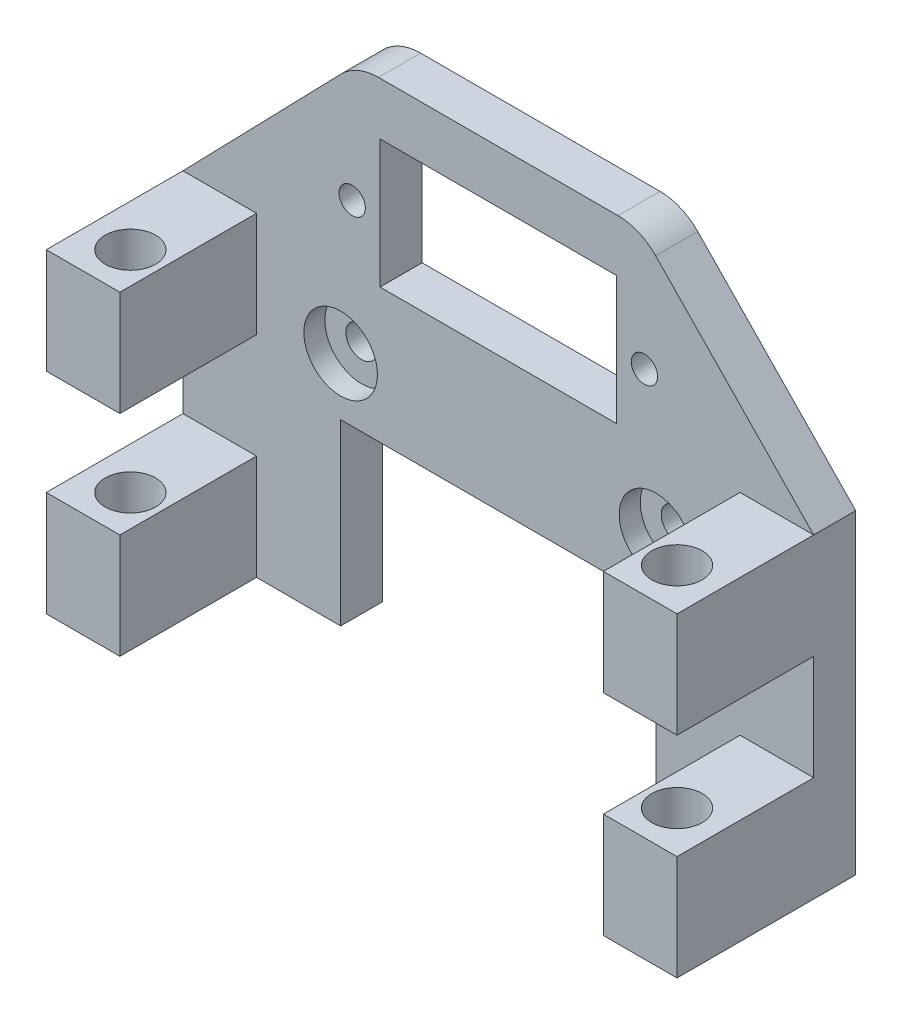
SolidWorks part; units mm, degrees
ref_plane "前视基准面" through (0, 0, 0) normal (0, 0, 1) x (1, 0, 0)
ref_plane "上视基准面" through (0, 0, 0) normal (0, 1, 0) x (1, 0, 0)
ref_plane "右视基准面" through (0, 0, 0) normal (1, 0, 0) x (0, 0, -1)
sketch "草图1" plane through (0, 0, 0) normal (0, 0, 1) x (1, 0, 0)
  line L0 (0, 28.504) -> (0, -24.2452) construction
  line L1 (-30, -15) -> (30, -15)
  line L2 (-30, -15) -> (-30, -2)
  line L3 (-13.5, 15) -> (13.5, 15)
  line L4 (30, -15) -> (30, -2)
  line L5 (-30, -15) -> (18.8911, 9.4455) construction
  line L6 (-18.8911, 9.4455) -> (30, -15) construction
  line L7 (-13.5, 15) -> (-30, -2)
  line L8 (13.5, 15) -> (30, -2)
  line L9 (-30, 15) -> (-13.5, 15) construction
  line L10 (-30, 15) -> (-18.8911, 9.4455) construction
  line L11 (-30, -2) -> (-30, 15) construction
  line L12 (13.5, 15) -> (30, 15) construction
  line L13 (18.8911, 9.4455) -> (30, 15) construction
  line L14 (30, -2) -> (30, 15) construction
  point P0 (0, 0)
  dimension "D1" = 60
  dimension "D2" = 30
  dimension "D3" = 16.5
  dimension "D4" = 17
extrude "凸台-拉伸1" add sketch "草图1" along normal blind 4
sketch "草图2" plane through (0, 0, 4) normal (0, 0, 1) x (1, 0, 0)
  line L0 (0, 18.5645) -> (0, 10) construction
  line L1 (11.25, 10) -> (11.25, -2.2)
  line L2 (-11.25, 10) -> (11.25, 10)
  line L3 (-11.25, 10) -> (-11.25, -2.2)
  line L4 (-11.25, -2.2) -> (11.25, -2.2)
  line L5 (0, 10) -> (0, -2.2) construction
  line L6 (0, 10) -> (0, -2.2) construction
  line L7 (0, -2.2) -> (0, -20.1622) construction
  line L8 (13.5, 15) -> (-13.5, 15) construction
  circle A0 centre (-13.9, 3.6107) radius 1.25
  circle A1 centre (13.9, 3.6107) radius 1.25
  circle A2 centre (-15, -9.5539) radius 1.5
  circle A3 centre (15, -9.5539) radius 1.5
  dimension "D4" = 2.5
  dimension "D6" = 3
  dimension "D1" = 22.5
  dimension "D2" = 12.2
  dimension "D3" = 5
  dimension "D5" = 27.8
  dimension "D7" = 30
extrude "切除-拉伸1" cut sketch "草图2" against normal through all
sketch "草图3" plane through (0, 0, 4) normal (0, 0, 1) x (1, 0, 0)
  line L0 (0, 19.6509) -> (0, -25.5302) construction
  line L1 (-30, -15) -> (-23, -15)
  line L2 (-30, -15) -> (-30, -2)
  line L3 (-30, -2) -> (-23, -2)
  line L4 (-23, -15) -> (-23, -2)
  line L5 (30, -2) -> (23, -2)
  line L6 (23, -15) -> (23, -2)
  line L7 (30, -15) -> (23, -15)
  line L8 (30, -15) -> (30, -2)
  dimension "D1" = 7
  dimension "D2" = 13
extrude "凸台-拉伸2" add sketch "草图3" along normal blind 13
sketch "草图4" plane through (0, -15, 0) normal (0, -1, 0) x (-1, 0, 0)
  line L0 (30, -17) -> (23, -17) construction
  line L2 (23, -17) -> (23, -4) construction
  line L3 (0, -22.1192) -> (0, 14.9459) construction
  circle A0 centre (26, -13) radius 2.15
  circle A1 centre (-26, -13) radius 2.15
  dimension "D1" = 4.3
  dimension "D2" = 4
  dimension "D3" = 3
extrude "切除-拉伸2" cut sketch "草图4" against normal through all both and the other way through all
fillet "圆角3" radius 5 2 edges at (13.5, 15, 2) (-13.5, 15, 2)
sketch "草图5" plane through (0, 0, 4) normal (0, 0, 1) x (1, 0, 0)
  circle A0 centre (-15, -9.5539) radius 3.5
  circle A1 centre (15, -9.5539) radius 3.5
  dimension "D1" = 7
  dimension "D2" = 7
extrude "切除-拉伸3" cut sketch "草图5" against normal blind 2
sketch "草图6" plane through (0, 0, 17) normal (0, 0, 1) x (1, 0, 0)
  line L0 (-23, -15) -> (-23, -2) construction
  line L1 (-30, -15) -> (-23, -15)
  line L2 (-30, -15) -> (-30, -12)
  line L3 (-30, -12) -> (-23, -12)
  line L4 (-23, -15) -> (-23, -12)
  line L5 (0, 64.8749) -> (0, -24.0964) construction
  line L6 (30, -12) -> (23, -12)
  line L7 (23, -15) -> (23, -12)
  line L8 (30, -15) -> (23, -15)
  line L9 (30, -15) -> (30, -12)
  point P11 (0, 20.3892)
  dimension "D1" = 3
extrude "切除-拉伸4" cut sketch "草图6" against normal blind 13
sketch "草图7" plane through (0, 0, 4) normal (0, 0, 1) x (1, 0, 0)
  line L1 (-30, -15) -> (-15, -15)
  line L2 (-30, -15) -> (-30, -32)
  line L3 (-30, -32) -> (-15, -32)
  line L4 (-15, -15) -> (-15, -32)
  line L5 (0, 92.2537) -> (0, -46.3979) construction
  line L6 (30, -32) -> (15, -32)
  line L7 (15, -15) -> (15, -32)
  line L8 (30, -15) -> (15, -15)
  line L9 (30, -15) -> (30, -32)
  point P5 (0, 22.9279)
  dimension "D1" = 17
  dimension "D2" = 15
extrude "凸台-拉伸3" add sketch "草图7" against normal blind 4
sketch "草图8" plane through (0, 0, 4) normal (0, 0, 1) x (1, 0, 0)
  line L0 (0, 88.1958) -> (0, -45.4789) construction
  line L1 (-30, -32) -> (-23, -32)
  line L2 (-30, -32) -> (-30, -22)
  line L3 (-30, -22) -> (-23, -22)
  line L4 (-23, -32) -> (-23, -22)
  line L5 (30, -22) -> (23, -22)
  line L6 (23, -32) -> (23, -22)
  line L7 (30, -32) -> (23, -32)
  line L8 (30, -32) -> (30, -22)
  point P9 (0, 21.3584)
  dimension "D1" = 10
  dimension "D2" = 7
extrude "凸台-拉伸4" add sketch "草图8" along normal blind 13
sketch "草图9" plane through (0, -32, 0) normal (0, -1, 0) x (1, 0, 0)
  line L0 (-23, 17) -> (-23, 4) construction
  line L1 (-30, 17) -> (-23, 17) construction
  line L2 (0, 86.9336) -> (0, -17.0967) construction
  circle A0 centre (-26, 13) radius 2.4
  circle A1 centre (26, 13) radius 2.4
  point P13 (0, 34.9184)
  dimension "D1" = 4.8
  dimension "D2" = 3
  dimension "D3" = 4
extrude "切除-拉伸5" cut sketch "草图9" against normal through all
